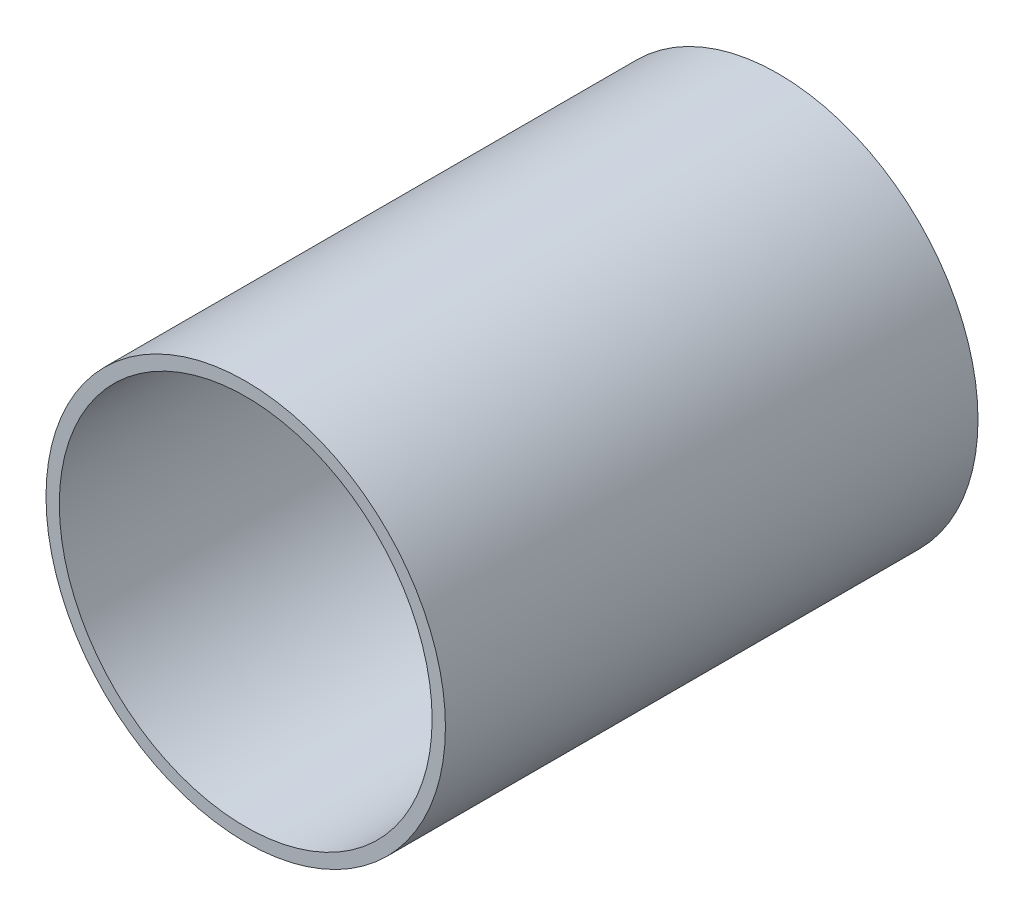
SolidWorks part; units mm, degrees
ref_plane "Plan de face" through (0, 0, 0) normal (0, 0, 1) x (1, 0, 0)
ref_plane "Plan de dessus" through (0, 0, 0) normal (0, 1, 0) x (1, 0, 0)
ref_plane "Plan de droite" through (0, 0, 0) normal (1, 0, 0) x (0, 0, -1)
sketch "Esquisse1" plane through (0, 0, 0) normal (0, 0, 1) x (1, 0, 0)
  circle A0 centre (0, 0) radius 75
  circle A1 centre (0, 0) radius 70
  dimension "D1" = 150
  dimension "D2" = 5
extrude "Boss.-Extru.1" add sketch "Esquisse1" along normal blind 200
sketch "Esquisse2" plane through (0, 0, 0) normal (0, 0, -1) x (-1, 0, 0)
  circle A0 centre (0, 0) radius 70 construction
  circle A1 centre (0, 0) radius 70
extrude "Boss.-Extru.2" add sketch "Esquisse2" against normal blind 5
